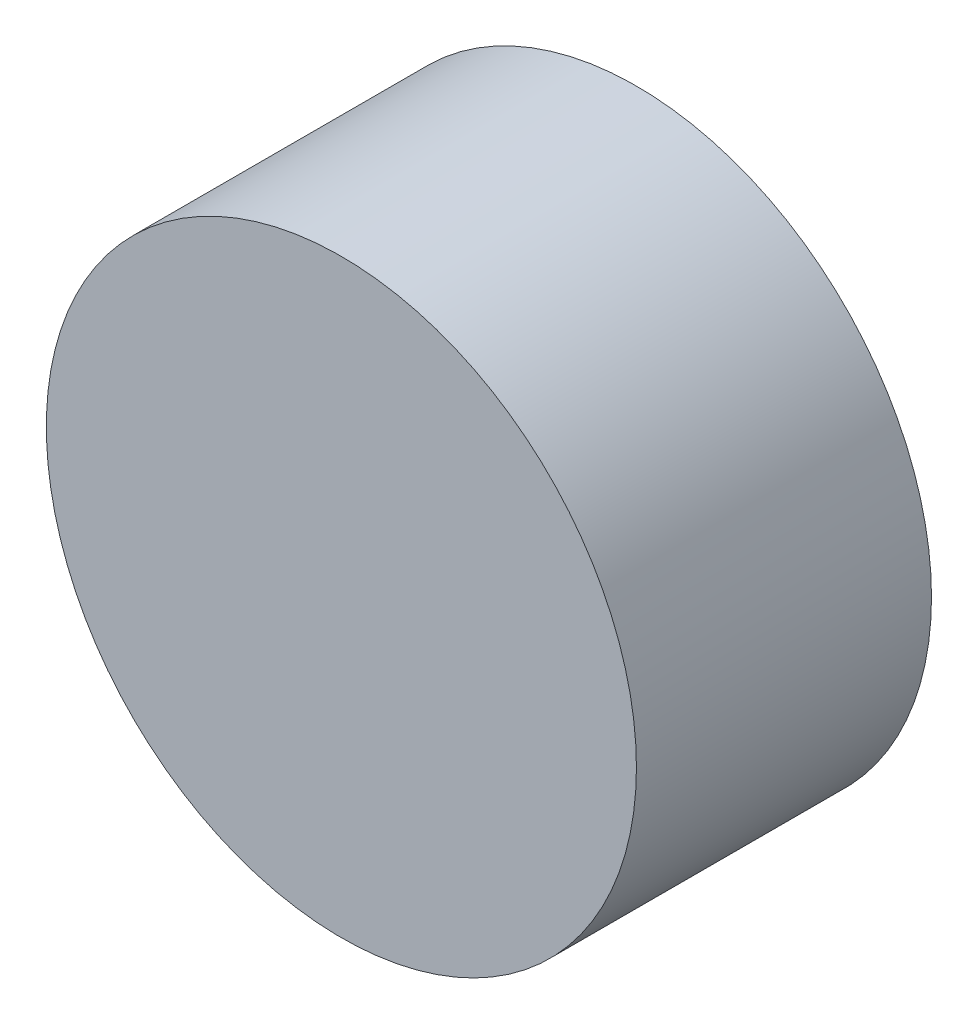
SolidWorks part; units mm, degrees
ref_plane "Front Plane" through (0, 0, 0) normal (0, 0, 1) x (1, 0, 0)
ref_plane "Top Plane" through (0, 0, 0) normal (0, 1, 0) x (1, 0, 0)
ref_plane "Right Plane" through (0, 0, 0) normal (1, 0, 0) x (0, 0, -1)
sketch "Sketch1" plane through (0, 0, 0) normal (0, 0, 1) x (1, 0, 0)
  circle A0 centre (0, 0) radius 50.8
  dimension "D1" = 101.6
extrude "Boss-Extrude1" add sketch "Sketch1" along normal blind 50.8
